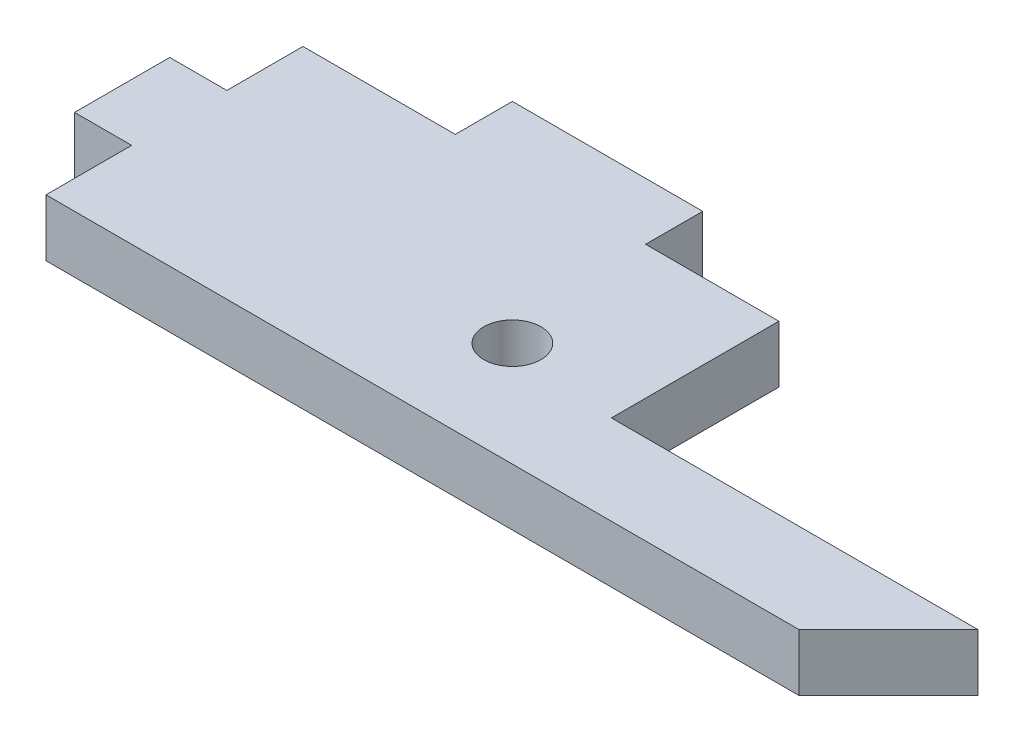
SolidWorks part; units mm, degrees
material "Acrylic (Medium-high impact)"
ref_plane "Front Plane" through (0, 0, 0) normal (0, 0, 1) x (1, 0, 0)
ref_plane "Top Plane" through (0, 0, 0) normal (0, 1, 0) x (1, 0, 0)
ref_plane "Right Plane" through (0, 0, 0) normal (1, 0, 0) x (0, 0, -1)
sketch "Sketch1" plane through (0, 0, 0) normal (0, 1, 0) x (1, 0, 0)
  line L1 (-37.889, 3.819) -> (-27.889, 3.819)
  line L2 (-1.629, -7.981) -> (-6.329, -12.681)
  line L3 (-6.329, -12.681) -> (-45.889, -12.681)
  line L4 (-27.889, 3.819) -> (-27.889, 0.819)
  line L5 (-27.889, 0.819) -> (-20.889, 0.819)
  line L8 (-45.889, -3.181) -> (-45.889, 0.819)
  line L9 (-45.889, -12.681) -> (-45.889, -8.181)
  line L10 (-20.889, 0.819) -> (-20.889, -7.981)
  line L11 (-20.889, -7.981) -> (-1.629, -7.981)
  line L12 (-45.889, 0.819) -> (-37.889, 0.819)
  line L13 (-37.889, 0.819) -> (-37.889, 3.819)
  line L14 (-45.889, -3.181) -> (-48.889, -3.181)
  line L15 (-48.889, -3.181) -> (-48.889, -8.181)
  line L16 (-48.889, -8.181) -> (-45.889, -8.181)
  circle A0 centre (-26.889, -7.181) radius 1.5
  dimension "D8" = 3
  dimension "D2" = 5
  dimension "D3" = 3
  dimension "D4" = 13.5
  dimension "D5" = 135
  dimension "D6" = 8
  dimension "D7" = 10
  dimension "D9" = 39.56
  dimension "D10" = 8.8
  dimension "D11" = 7
  dimension "D12" = 4
  dimension "D13" = 8
  dimension "D14" = 22
extrude "Boss-Extrude1" add sketch "Sketch1" along normal blind 3
